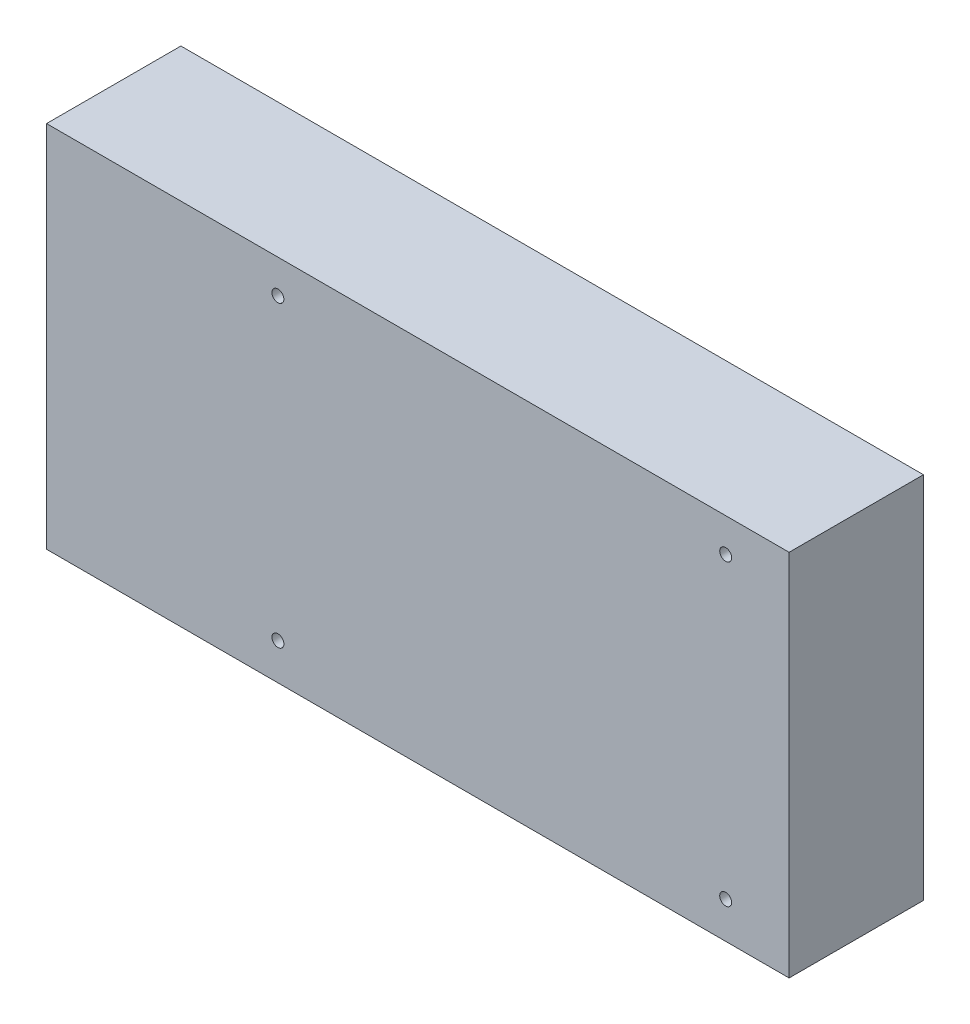
SolidWorks part; units mm, degrees
ref_plane "Front Plane" through (0, 0, 0) normal (0, 0, 1) x (1, 0, 0)
ref_plane "Top Plane" through (0, 0, 0) normal (0, 1, 0) x (1, 0, 0)
ref_plane "Right Plane" through (0, 0, 0) normal (1, 0, 0) x (0, 0, -1)
sketch "Sketch1" plane through (0, 0, 0) normal (0, 0, 1) x (1, 0, 0)
  line L1 (-99.5, -49.403) -> (99.5, -49.403)
  line L2 (-99.5, -49.403) -> (-99.5, 49.403)
  line L3 (-99.5, 49.403) -> (99.5, 49.403)
  line L4 (99.5, -49.403) -> (99.5, 49.403)
  line L5 (-99.5, -49.403) -> (99.5, 49.403) construction
  line L6 (-99.5, 49.403) -> (99.5, -49.403) construction
  point P0 (0, 0)
  dimension "D1" = 199
  dimension "D2" = 98.806
extrude "Boss-Extrude1" add sketch "Sketch1" along normal blind 36
sketch "Sketch2" plane through (0, 0, 36) normal (0, 0, 1) x (1, 0, 0)
  line L0 (-99.5, 49.403) -> (-99.5, -49.403) construction
  line L1 (99.5, 49.403) -> (-99.5, 49.403) construction
  circle A0 centre (-37.5, 40.403) radius 1.6
  dimension "D2" = 3.2
  dimension "D1" = 62
  dimension "D3" = 9
extrude "Cut-Extrude1" cut sketch "Sketch2" against normal through all
pattern_linear "LPattern1" count 2 spacing 120 along (1, 0, 0) count 2 spacing 80 along (0, -1, 0) of "Cut-Extrude1"
